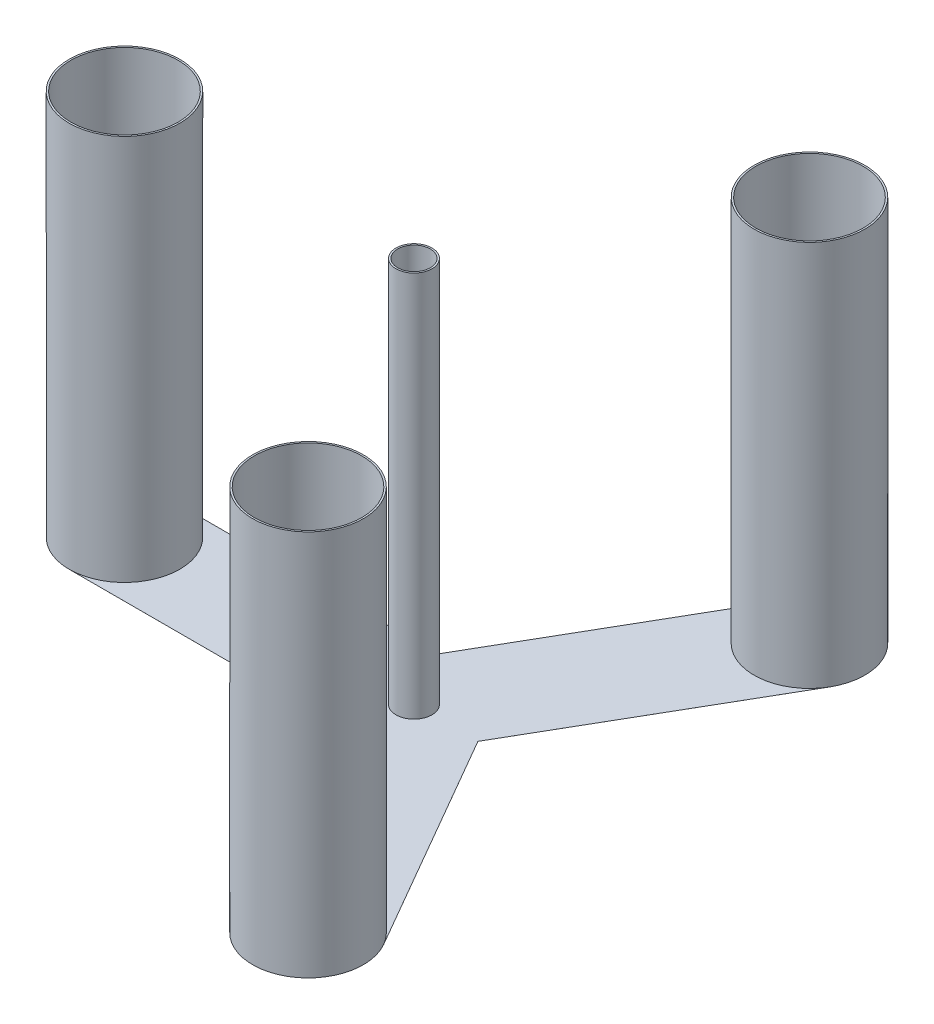
SolidWorks part; units mm, degrees
material "PVC Rigid"
ref_plane "Front Plane" through (0, 0, 0) normal (0, 0, 1) x (1, 0, 0)
ref_plane "Top Plane" through (0, 0, 0) normal (0, 1, 0) x (1, 0, 0)
ref_plane "Right Plane" through (0, 0, 0) normal (1, 0, 0) x (0, 0, -1)
sketch "Sketch1" plane through (0, 0, 0) normal (0, 1, 0) x (1, 0, 0)
  line L0 (-37.2391, 64.5) -> (-337.2391, 64.5)
  line L3 (-337.2391, -64.5) -> (-37.2391, -64.5)
  line L6 (-37.2391, 64.5) -> (112.7609, 324.3076)
  line L7 (224.4782, 259.8076) -> (74.4782, 0)
  line L8 (74.4782, 0) -> (224.4782, -259.8076)
  line L9 (112.7609, -324.3076) -> (-37.2391, -64.5)
  arc A4 (-337.2391, -64.5) -> (-337.2391, 64.5) centre (-337.2391, 0) cw
  arc A5 (112.7609, 324.3076) -> (224.4782, 259.8076) centre (168.6195, 292.0576) cw
  arc A6 (224.4782, -259.8076) -> (112.7609, -324.3076) centre (168.6195, -292.0576) cw
  dimension "D6" = 64.5
  dimension "D10" = 64.5
  dimension "D15" = 64.5
  dimension "D2" = 64.5
  dimension "D4" = 120
  dimension "D5" = 300
  dimension "D3" = 300
  dimension "D8" = 120
  dimension "D9" = 120
  dimension "D11" = 300
  dimension "D12" = 300
  dimension "D13" = 300
  dimension "D7" = 0
  dimension "D14" = 64.5
extrude "Boss-Extrude1" add sketch "Sketch1" along normal blind 0.01
sketch "Sketch2" plane through (0, 0.01, 0) normal (0, 1, 0) x (1, 0, 0)
  circle A1 centre (168.6195, 292.0576) radius 64.5
  circle A2 centre (-337.2391, 0) radius 64.5
  circle A4 centre (168.6195, -292.0576) radius 64.5
  circle A5 centre (0, 0) radius 21
  circle A6 centre (168.6195, -292.0576) radius 62.5
  circle A7 centre (0, 0) radius 19
  circle A8 centre (-337.2391, 0) radius 62.5
  circle A9 centre (168.6195, 292.0576) radius 62.5
  dimension "D1" = 42
  dimension "D2" = 2
  dimension "D3" = 2
  dimension "D4" = 2
  dimension "D5" = 2
extrude "Boss-Extrude2" add sketch "Sketch2" along normal blind 450
sketch "Sketch4" plane through (0, 450.01, 0) normal (0, 1, 0) x (1, 0, 0)
  line L0 (-337.2391, -64.5) -> (-37.2391, -64.5)
  line L1 (-37.2391, -64.5) -> (112.7609, -324.3076)
  line L2 (224.4782, -259.8076) -> (74.4782, 0)
  line L3 (-337.2391, 64.5) -> (-37.2391, 64.5)
  line L4 (-37.2391, 64.5) -> (112.7609, 324.3076)
  line L5 (74.4782, 0) -> (224.4782, 259.8076)
  circle A0 centre (-337.2391, 0) radius 64.5 construction
  circle A1 centre (168.6195, -292.0576) radius 64.5 construction
  arc A2 (112.7609, -324.3076) -> (224.4782, -259.8076) centre (168.6195, -292.0576) ccw
  arc A3 (-337.2391, -64.5) -> (-337.2391, 64.5) centre (-337.2391, 0) cw
  circle A4 centre (168.6195, 292.0576) radius 64.5 construction
  arc A5 (112.7609, 324.3076) -> (224.4782, 259.8076) centre (168.6195, 292.0576) cw
  dimension "D5" = 300
  dimension "D3" = 300
  dimension "D1" = 300
  dimension "D2" = 300
  dimension "D4" = 64.5
  dimension "D6" = 300
  dimension "D7" = 64.5
  dimension "D8" = 0
equation "\"length\"=300"
equation "\"D12@Sketch1\"=\"length\""
equation "\"D13@Sketch1\"=\"length\""
equation "\"D3@Sketch1\"=\"length\""
equation "\"D11@Sketch1\"=\"length\""
equation "\"D5@Sketch1\"=\"length\""
equation "\"radius\"=64.5"
equation "\"D10@Sketch1\"=\"radius\""
equation "\"D14@Sketch1\"=\"radius\""
equation "\"D15@Sketch1\"=\"radius\""
equation "\"D6@Sketch1\"=\"radius\""
equation "\"D2@Sketch1\"=\"radius\""
equation "\"D4@Sketch4\"=\"radius\""
equation "\"D1@Sketch4\"=\"length\""
equation "\"D2@Sketch4\"=\"length\""
equation "\"D3@Sketch4\"=\"length\""
equation "\"D5@Sketch4\"=\"length\""
equation "\"D6@Sketch4\"=\"length\""
equation "\"D7@Sketch4\"=\"radius\""
equation "\"heave\"=120"
